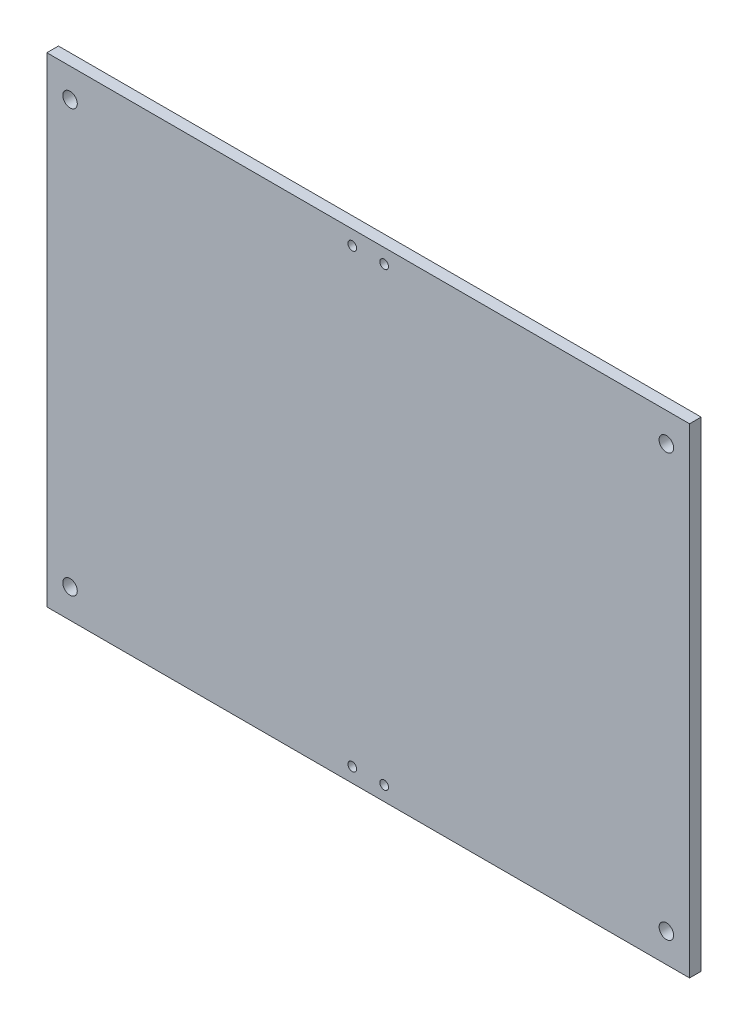
SolidWorks part; units mm, degrees
ref_plane "Front Plane" through (0, 0, 0) normal (0, 0, 1) x (1, 0, 0)
ref_plane "Top Plane" through (0, 0, 0) normal (0, 1, 0) x (1, 0, 0)
ref_plane "Right Plane" through (0, 0, 0) normal (1, 0, 0) x (0, 0, -1)
sketch "Sketch1" plane through (0, 0, 0) normal (0, 0, 1) x (1, 0, 0)
  line L1 (389.3975, 431.4754) -> (611.1475, 431.4754)
  line L2 (389.3975, 431.4754) -> (389.3975, 265.8654)
  line L3 (389.3975, 265.8654) -> (611.1475, 265.8654)
  line L4 (611.1475, 431.4754) -> (611.1475, 265.8654)
  dimension "D1" = 221.75
  dimension "D2" = 165.61
extrude "Boss-Extrude1" add sketch "Sketch1" along normal blind 4
sketch "Sketch3" plane through (0, 0, 4) normal (0, 0, 1) x (1, 0, 0)
  line L0 (389.3975, 431.4754) -> (389.3975, 265.8654) construction
  line L1 (611.1475, 265.8654) -> (611.1475, 431.4754) construction
  line L2 (611.1475, 431.4754) -> (389.3975, 431.4754) construction
  line L3 (389.3975, 265.8654) -> (611.1475, 265.8654) construction
  circle A0 centre (397.3975, 421.4754) radius 2.5
  circle A1 centre (603.1475, 421.4754) radius 2.5
  circle A2 centre (603.1475, 275.8654) radius 2.5
  circle A3 centre (397.3975, 275.8654) radius 2.5
  dimension "D7" = 5
  dimension "D8" = 5
  dimension "D9" = 5
  dimension "D10" = 5
  dimension "D1" = 8
  dimension "D2" = 8
  dimension "D3" = 10
  dimension "D4" = 10
  dimension "D5" = 8
  dimension "D6" = 10
  dimension "D11" = 10
  dimension "D12" = 8
extrude "Cut-Extrude1" cut sketch "Sketch3" against normal through all
sketch "Sketch4" plane through (0, 0, 4) normal (0, 0, 1) x (1, 0, 0)
  line L0 (389.3975, 265.8654) -> (611.1475, 265.8654) construction
  line L1 (494.7725, 270.8654) -> (505.7725, 270.8654) construction
  line L2 (500.2725, 265.8654) -> (500.2725, 431.4754) construction
  line L3 (611.1475, 431.4754) -> (389.3975, 431.4754) construction
  circle A0 centre (494.7725, 270.8654) radius 1.5
  circle A1 centre (505.7725, 270.8654) radius 1.5
  circle A2 centre (494.7725, 426.4754) radius 1.5
  circle A3 centre (505.7725, 426.4754) radius 1.5
  point P6 (500.2725, 270.8654)
  dimension "D2" = 3
  dimension "D3" = 3
  dimension "D6" = 3
  dimension "D7" = 3
  dimension "D1" = 11
  dimension "D4" = 5
  dimension "D5" = 5
extrude "Cut-Extrude2" cut sketch "Sketch4" against normal blind 10
equation "\"HorizontalDistance\"= 8"
equation "\"VerticalDistance\"= 10"
equation "\"D1@Sketch3\"=\"HorizontalDistance\""
equation "\"D2@Sketch3\"=\"HorizontalDistance\""
equation "\"D3@Sketch3\"=\"VerticalDistance\""
equation "\"D4@Sketch3\"=\"VerticalDistance\""
equation "\"D5@Sketch3\"=\"HorizontalDistance\""
equation "\"D6@Sketch3\"=\"VerticalDistance\""
equation "\"D11@Sketch3\"=\"VerticalDistance\""
equation "\"D12@Sketch3\"=\"HorizontalDistance\""
equation "\"D3@Sketch4\"=\"D2@Sketch4\""
equation "\"D5@Sketch4\"=\"D4@Sketch4\""
equation "\"D6@Sketch4\"=\"D2@Sketch4\""
equation "\"D7@Sketch4\"=\"D2@Sketch4\""
